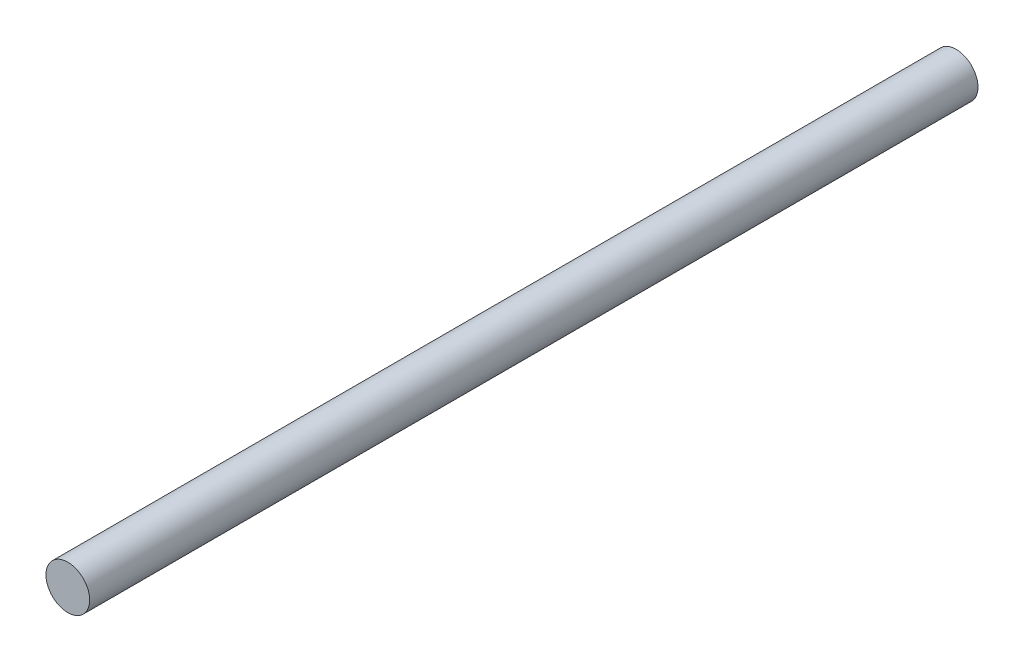
SolidWorks part; units mm, degrees
ref_plane "Front Plane" through (0, 0, 0) normal (0, 0, 1) x (1, 0, 0)
ref_plane "Top Plane" through (0, 0, 0) normal (0, 1, 0) x (1, 0, 0)
ref_plane "Right Plane" through (0, 0, 0) normal (1, 0, 0) x (0, 0, -1)
sketch "Esquisse1" plane through (0, 0, 0) normal (0, 0, 1) x (1, 0, 0)
  circle A0 centre (0, 0) radius 1.6
  dimension "D1" = 3.2
extrude "Main" add sketch "Esquisse1" along normal blind 65
